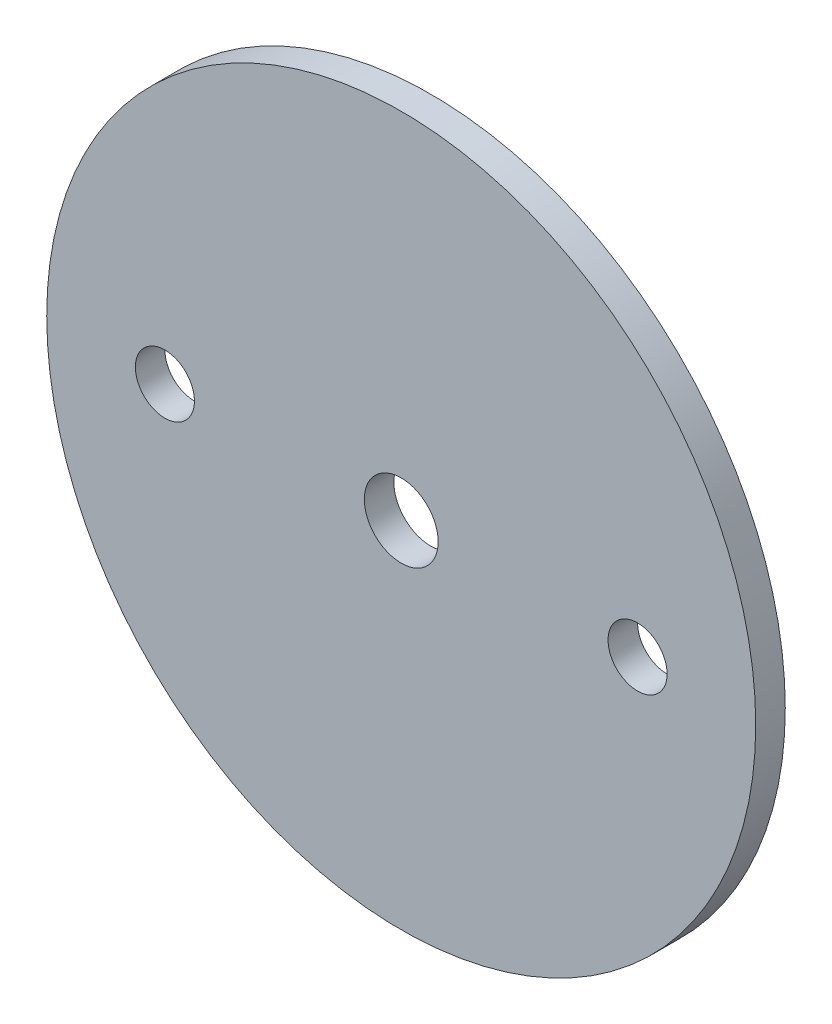
SolidWorks part; units mm, degrees
ref_plane "Front Plane" through (0, 0, 0) normal (0, 0, 1) x (1, 0, 0)
ref_plane "Top Plane" through (0, 0, 0) normal (0, 1, 0) x (1, 0, 0)
ref_plane "Right Plane" through (0, 0, 0) normal (1, 0, 0) x (0, 0, -1)
sketch "Sketch1" plane through (0, 0, 0) normal (0, 0, 1) x (1, 0, 0)
  circle A0 centre (0, 0) radius 38.1
  dimension "D1" = 76.2
extrude "Boss-Extrude1" add sketch "Sketch1" along normal mid plane 3.175
sketch "Sketch2" plane through (0, 0, 1.5875) normal (0, 0, 1) x (1, 0, 0)
  line L0 (-1000, 0) -> (49000, 0) construction
  line L1 (0, -1000) -> (0, 49000) construction
  point P4 (25.4, 0)
  point P5 (-25.4, 0)
  dimension "D2" = 50.8
  dimension "D1" = 25.4
hole_wizard "1/4 (0.25) Diameter Hole1" positions "Sketch2" profile "Sketch3" hole size "1/4" standard "ANSI Inch" end condition through all
sketch "Sketch3" plane through (-25.4, 0, 1.5875) normal (1, 0, 0) x (0, -1, 0)
  line L0 (0, 0) -> (0, 3.175)
  line L1 (0, 3.175) -> (3.175, 3.175)
  line L2 (3.175, 3.175) -> (3.175, 0)
  line L5 (3.175, 0) -> (0, 0)
  line L11 (0, -6.35) -> (0, 107.95) construction
  dimension "Thru Hole Dia." = 6.35
  dimension "Thru Hole Depth" = 3.175
sketch "Sketch4" plane through (0, 0, 1.5875) normal (0, 0, 1) x (1, 0, 0)
  point P0 (0, 0)
hole_wizard "5/16 (0.3125) Diameter Hole1" positions "Sketch4" profile "Sketch5" hole size "5/16" standard "ANSI Inch"
sketch "Sketch5" plane through (0, 0, 1.5875) normal (1, 0, 0) x (0, -1, 0)
  line L0 (0, 0) -> (0, 3.302)
  line L1 (0, 3.302) -> (3.9687, 3.302)
  line L2 (3.9687, 3.302) -> (3.9688, 0)
  line L5 (3.9688, 0) -> (0, 0)
  line L10 (0, 3.302) -> (-3.9688, 3.302) construction
  line L11 (0, -6.35) -> (0, 107.95) construction
  dimension "Hole Dia." = 7.9375
  dimension "Hole Depth" = 3.302
  dimension "Drill Angle" = 180
equation "\"AIRFRAME_OD\"= 3.091in"
equation "\"AIRFRAME_ID\"= 3.00in"
equation "\"FLAT_T\"= 0.125in"
equation "\"NOSE_EXP_L\"= 3.5in"
equation "\"NOSE_SHOULDER_L\"= 5in"
equation "\"MAIN_L\"= 30in"
equation "\"RECO_COUP_L\"= 6in"
equation "\"RECO_SWITCH_L\"= 1.5in"
equation "\"DROGUE_L\"= 14in"
equation "\"ATS_FORE_COUP_L\"= 4in"
equation "\"ATS_AFT_COUP_L\"= 2.5in"
equation "\"LOWER_L\"= 16in"
equation "\"FIN_N\"= 4"
equation "\"CR_AFT_X\"= 0.5in"
equation "\"CR_FORE_X\"= 6in"
equation "\"FIN_ROOT\"= 5in"
equation "\"FIN_X\"= 0.75in"
equation "\"MOTOR_OD\"= 2.25in"
equation "\"MOTOR_ID\"= 2.126in"
equation "\"COUPLER_OD\"= 2.998in"
equation "\"COUPLER_ID\"= 2.875in"
equation "\"D1@Sketch1\"=\"AIRFRAME_ID\""
equation "\"D1@Boss-Extrude1\"=\"FLAT_T\""
equation "\"RECO_ROD_X\"= 1.5in"
equation "\"ATS_ROD_X\"= 2in"
equation "\"D2@Sketch2\"=\"ATS_ROD_X\""
